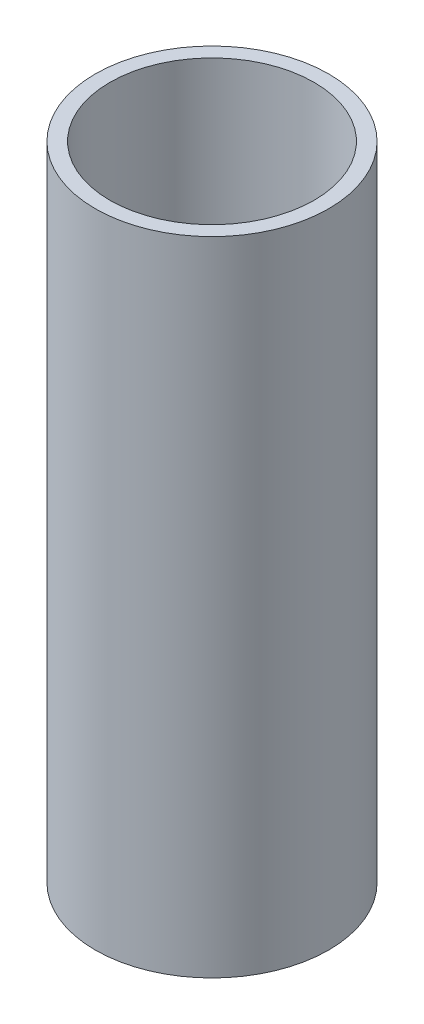
SolidWorks part; units mm, degrees
material "Kraft"
ref_plane "Plan de face" through (0, 0, 0) normal (0, 0, 1) x (1, 0, 0)
ref_plane "Plan de dessus" through (0, 0, 0) normal (0, 1, 0) x (1, 0, 0)
ref_plane "Plan de droite" through (0, 0, 0) normal (1, 0, 0) x (0, 0, -1)
sketch "Esquisse2" plane through (0, 0, 0) normal (0, 1, 0) x (1, 0, 0)
  circle A0 centre (0, 0) radius 12
  circle A1 centre (0, 0) radius 10.5
  dimension "D1" = 24
  dimension "D2" = 21
extrude "Boss.-Extru.1" add sketch "Esquisse2" along normal mid plane 66
